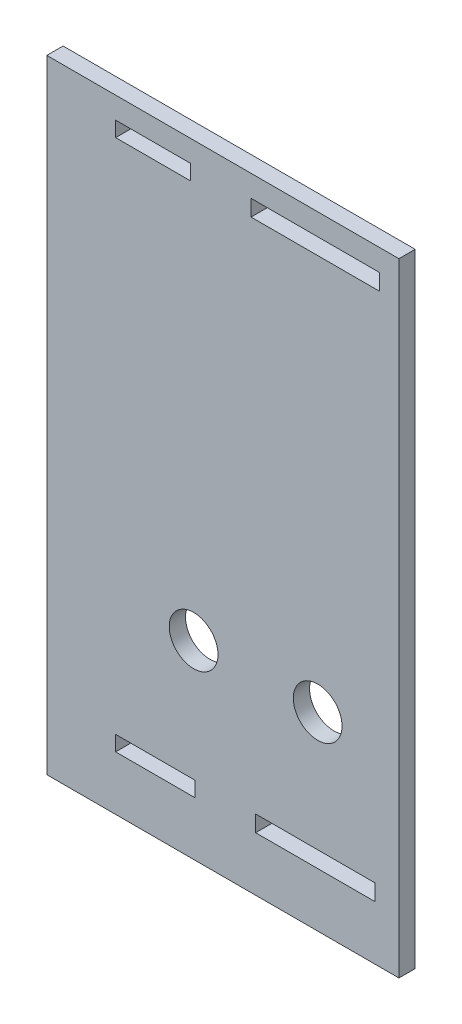
SolidWorks part; units mm, degrees
ref_plane "Alzado" through (0, 0, 0) normal (0, 0, 1) x (1, 0, 0)
ref_plane "Planta" through (0, 0, 0) normal (0, 1, 0) x (1, 0, 0)
ref_plane "Vista lateral" through (0, 0, 0) normal (1, 0, 0) x (0, 0, -1)
sketch "Croquis1" plane through (0, 0, 0) normal (0, 0, 1) x (1, 0, 0)
  line L0 (-50, -47.5) -> (50, -47.5) construction
  line L1 (50, -57.5) -> (-50, -57.5)
  line L2 (50, -57.5) -> (50, 57.5)
  line L3 (50, 57.5) -> (-50, 57.5)
  line L4 (-50, -57.5) -> (-50, 57.5)
  line L5 (50, -57.5) -> (-50, 57.5) construction
  line L6 (50, 57.5) -> (-50, -57.5) construction
  line L7 (0, 57.5) -> (0, -57.5) construction
  line L8 (22.6, -47.5) -> (37.3, -47.5)
  line L9 (22.6, -47.5) -> (22.6, -44.7)
  line L10 (22.6, -44.7) -> (37.3, -44.7)
  line L11 (37.3, -47.5) -> (37.3, -44.7)
  line L12 (-37.3, -47.5) -> (-37.3, -44.7)
  line L13 (-22.6, -44.7) -> (-37.3, -44.7)
  line L14 (-22.6, -47.5) -> (-22.6, -44.7)
  line L15 (-22.6, -47.5) -> (-37.3, -47.5)
  line L16 (-50, 0) -> (50, 0) construction
  line L17 (-11.45, -47.5) -> (10.6, -47.5)
  line L18 (-11.45, -47.5) -> (-11.45, -44.5)
  line L19 (-11.45, -44.5) -> (10.6, -44.5)
  line L20 (10.6, -47.5) -> (10.6, -44.5)
  line L33 (37.3, 50.7) -> (23.45, 50.7)
  line L34 (-37.3, 53.5) -> (-23.45, 53.5)
  line L35 (-37.3, 53.5) -> (-37.3, 50.7)
  line L36 (-37.3, 50.7) -> (-23.45, 50.7)
  line L37 (-23.45, 53.5) -> (-23.45, 50.7)
  line L38 (23.45, 53.5) -> (23.45, 50.7)
  line L39 (37.3, 53.5) -> (23.45, 53.5)
  line L40 (37.3, 53.5) -> (37.3, 50.7)
  line L42 (-12.3, 53.5) -> (11.45, 53.5)
  line L43 (-12.3, 53.5) -> (-12.3, 50.5)
  line L44 (-12.3, 50.5) -> (11.45, 50.5)
  line L45 (11.45, 53.5) -> (11.45, 50.5)
  circle A0 centre (0, -22.5) radius 4.5
  circle A1 centre (-22.9, -22.5) radius 4.5
  circle A2 centre (24.1, -22.5) radius 4.5
  point P0 (0, 0)
  point P37 (23.45, 52.1)
  dimension "D18" = 9
  dimension "D20" = 9
  dimension "D21" = 9
  dimension "D1" = 115
  dimension "D2" = 100
  dimension "D3" = 10
  dimension "D4" = 12.7
  dimension "D5" = 14.7
  dimension "D6" = 2.8
  dimension "D7" = 11.15
  dimension "D8" = 12
  dimension "D9" = 3
  dimension "D10" = 4
  dimension "D11" = 12.7
  dimension "D12" = 2.8
  dimension "D13" = 11.15
  dimension "D14" = 12
  dimension "D15" = 4
  dimension "D16" = 95
  dimension "D17" = 38.55
  dimension "D19" = 35
  dimension "D22" = 22.9
  dimension "D23" = 47
  dimension "D24" = 35
  dimension "D25" = 35
extrude "Saliente-Extruir1" add sketch "Croquis1" along normal blind 3
sketch "Croquis2" plane through (0, 0, 3) normal (0, 0, 1) x (1, 0, 0)
  line L5 (-50, -57.5) -> (50, -57.5) construction
  line L6 (50, 57.5) -> (15, 57.5)
  line L7 (50, 57.5) -> (50, -57.5)
  line L8 (50, -57.5) -> (15, -57.5)
  line L9 (15, 57.5) -> (15, -57.5)
  dimension "D1" = 35
extrude "Cortar-Extruir1" cut sketch "Croquis2" against normal through all
